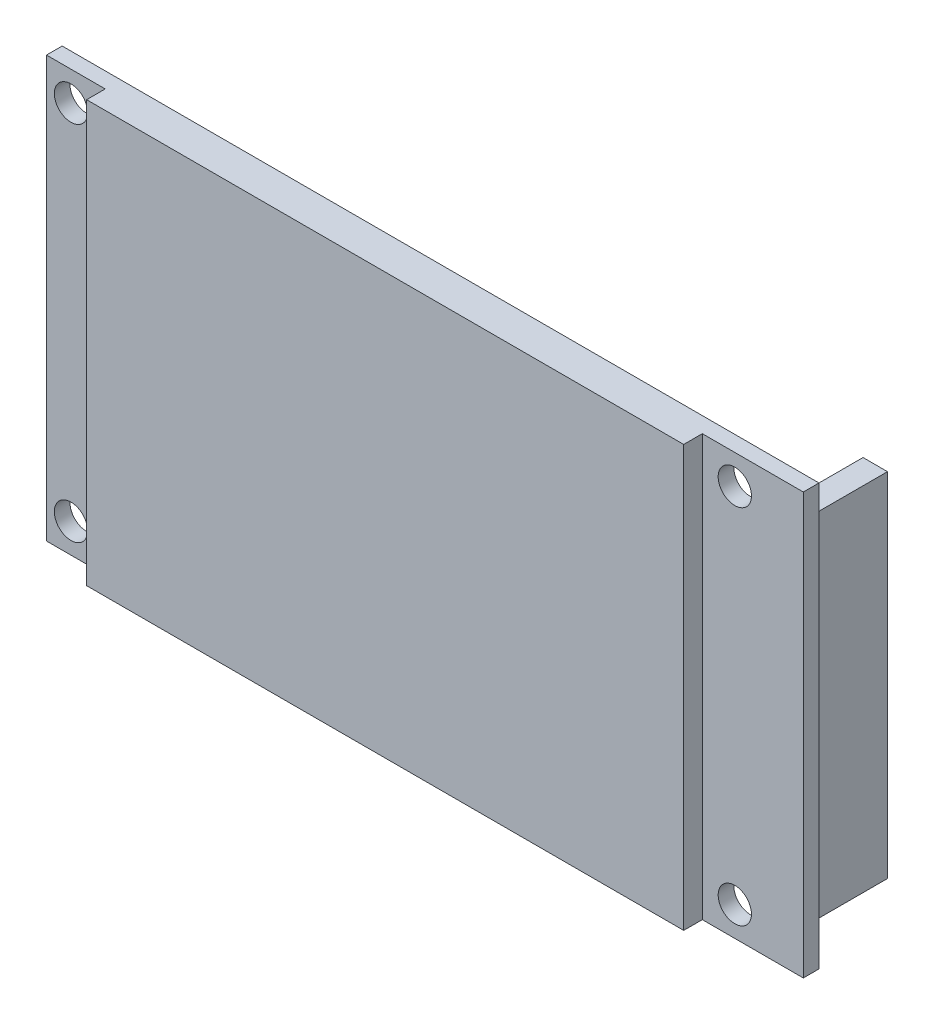
SolidWorks part; units mm, degrees
ref_plane "Top" through (0, 0, 0) normal (0, 0, 1) x (1, 0, 0)
ref_plane "Front" through (0, 0, 0) normal (0, 1, 0) x (1, 0, 0)
ref_plane "Right Plane" through (0, 0, 0) normal (1, 0, 0) x (0, 0, -1)
sketch "Sketch1" plane through (0, 0, 0) normal (0, 0, 1) x (1, 0, 0)
  line L1 (0, 0) -> (77.32, 0)
  line L2 (0, 0) -> (0, 43)
  line L3 (0, 43) -> (77.32, 43)
  line L4 (77.32, 0) -> (77.32, 43)
  circle A0 centre (70.32, 40) radius 1.7
  circle A1 centre (70.32, 3) radius 1.7
  circle A2 centre (2.5, 3) radius 1.7
  circle A3 centre (2.5, 40) radius 1.7
  dimension "D3" = 3.4
  dimension "D4" = 3.4
  dimension "D7" = 3.4
  dimension "D8" = 3.4
  dimension "D1" = 77.32
  dimension "D2" = 43
  dimension "D5" = 3
  dimension "D6" = 3
  dimension "D9" = 3
  dimension "D10" = 3
  dimension "D11" = 7
  dimension "D12" = 2.5
  dimension "D13" = 7
  dimension "D14" = 2.5
extrude "Boss-Extrude1" add sketch "Sketch1" along normal blind 1.6
sketch "Sketch3" plane through (0, 0, 0) normal (0, 0, -1) x (-1, 0, 0)
  line L0 (0, 0) -> (-77.32, 0) construction
  line L1 (-6, 0) -> (-67, 0)
  line L2 (-6, 0) -> (-6, 43)
  line L3 (-6, 43) -> (-67, 43)
  line L4 (-67, 0) -> (-67, 43)
  line L5 (-77.32, 43) -> (0, 43) construction
  line L7 (0, 43) -> (0, 0) construction
  dimension "D1" = 61
  dimension "D2" = 6
extrude "Boss-Extrude3" add sketch "Sketch3" against normal blind 3.5
sketch "Sketch4" plane through (0, 0, 0) normal (0, 0, -1) x (-1, 0, 0)
  line L1 (-76.32, 39.5) -> (-73.82, 39.5)
  line L2 (-76.32, 39.5) -> (-76.32, 3.5)
  line L3 (-76.32, 3.5) -> (-73.82, 3.5)
  line L4 (-73.82, 39.5) -> (-73.82, 3.5)
  line L5 (-3.5, 27) -> (-1, 27)
  line L6 (-3.5, 27) -> (-3.5, 16)
  line L7 (-3.5, 16) -> (-1, 16)
  line L8 (-1, 27) -> (-1, 16)
  line L9 (-77.32, 0) -> (-77.32, 43) construction
  line L10 (-77.32, 43) -> (0, 43) construction
  line L13 (0, 43) -> (0, 0) construction
  dimension "D1" = 2.5
  dimension "D2" = 2.5
  dimension "D3" = 36
  dimension "D4" = 1
  dimension "D5" = 3.5
  dimension "D6" = 11
  dimension "D7" = 16
  dimension "D8" = 1
extrude "Boss-Extrude4" add sketch "Sketch4" along normal blind 8
